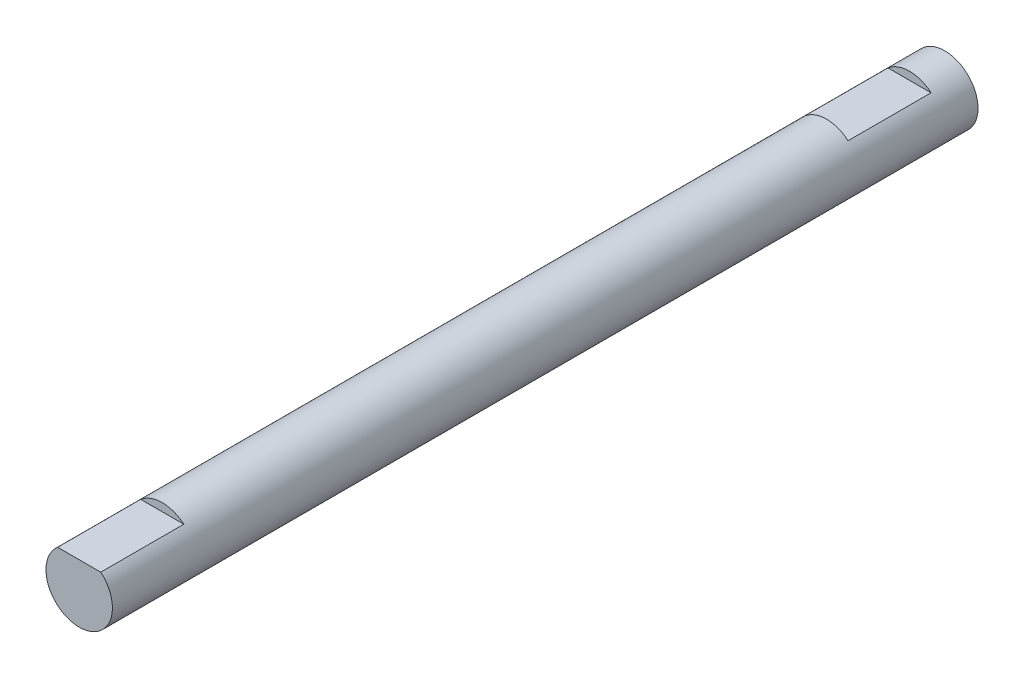
SolidWorks part; units mm, degrees
ref_plane "前视基准面" through (0, 0, 0) normal (0, 0, 1) x (1, 0, 0)
ref_plane "上视基准面" through (0, 0, 0) normal (0, 1, 0) x (1, 0, 0)
ref_plane "右视基准面" through (0, 0, 0) normal (1, 0, 0) x (0, 0, -1)
sketch "草图1" plane through (0, 0, 0) normal (0, 0, 1) x (1, 0, 0)
  circle A0 centre (2.7888, 15.199) radius 4
extrude "凸台-拉伸1" add sketch "草图1" along normal blind 104.25
sketch "草图2" plane through (0, 0, 104.25) normal (0, 0, 1) x (1, 0, 0)
  line L0 (-1.2112, 18.2412) -> (6.7888, 18.2412)
  line L1 (6.7888, 18.2412) -> (6.7888, 20.4906)
  line L2 (6.7888, 20.4906) -> (-1.3535, 20.4906)
  line L3 (-1.3535, 20.4906) -> (-1.4518, 18.2412)
  line L4 (-1.4518, 18.2412) -> (-1.2112, 18.2412)
extrude "切除-拉伸1" cut sketch "草图2" against normal blind 10
ref_plane "基准面1" through (0, 0, 54.25) normal (0, 0, 1) x (1, 0, 0)
mirror "镜向1" about plane through (0, 0, 54.25) normal (0, 0, 1) of "切除-拉伸1"
